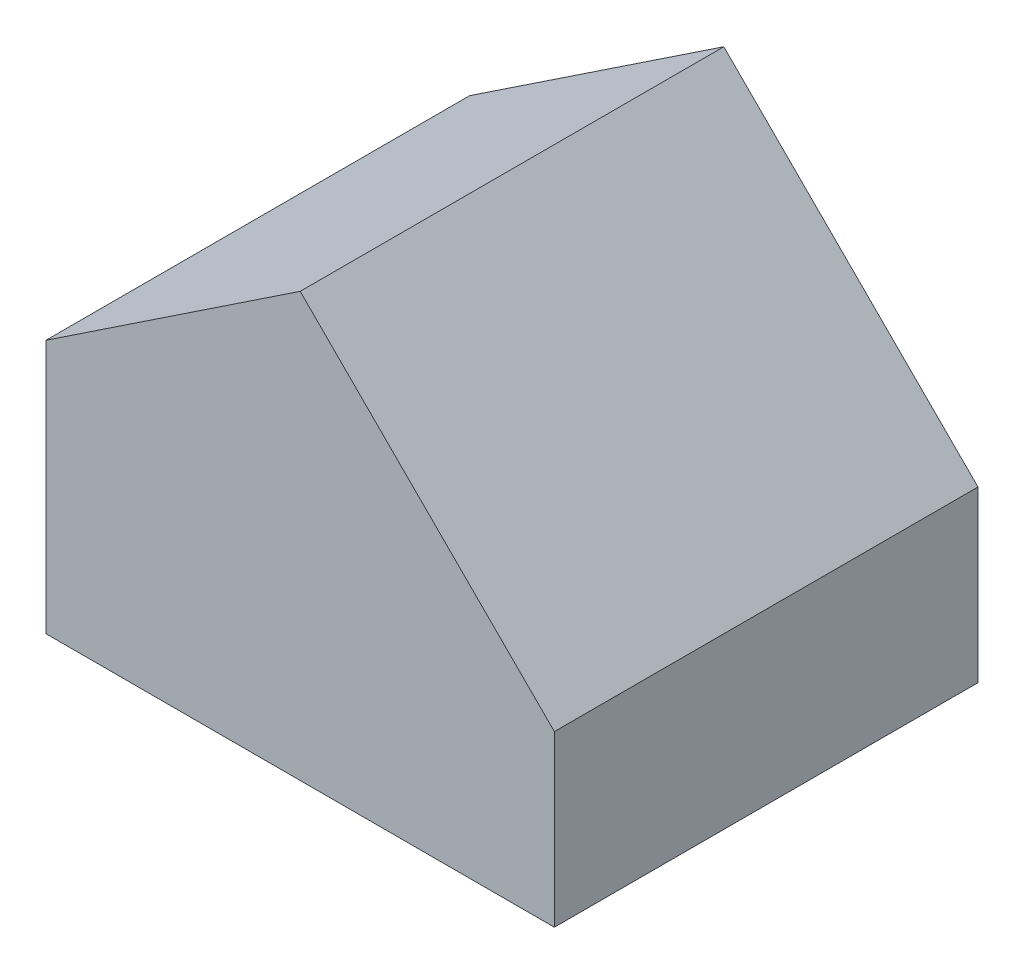
SolidWorks part; units mm, degrees
ref_plane "Front Plane" through (0, 0, 0) normal (0, 0, 1) x (1, 0, 0)
ref_plane "Top Plane" through (0, 0, 0) normal (0, 1, 0) x (1, 0, 0)
ref_plane "Right Plane" through (0, 0, 0) normal (1, 0, 0) x (0, 0, -1)
sketch "Sketch1" plane through (0, 0, 0) normal (0, 0, 1) x (1, 0, 0)
  line L0 (-30, 15) -> (-15, 25)
  line L1 (-15, 25) -> (0, 10)
  line L2 (0, 10) -> (0, 0)
  line L3 (0, 0) -> (-30, 0)
  line L4 (-30, 0) -> (-30, 15)
  point P2 (-15, 15)
  dimension "D1" = 30
  dimension "D2" = 10
  dimension "D3" = 15
  dimension "D4" = 15
  dimension "D5" = 10
extrude "Boss-Extrude1" add sketch "Sketch1" along normal blind 25
